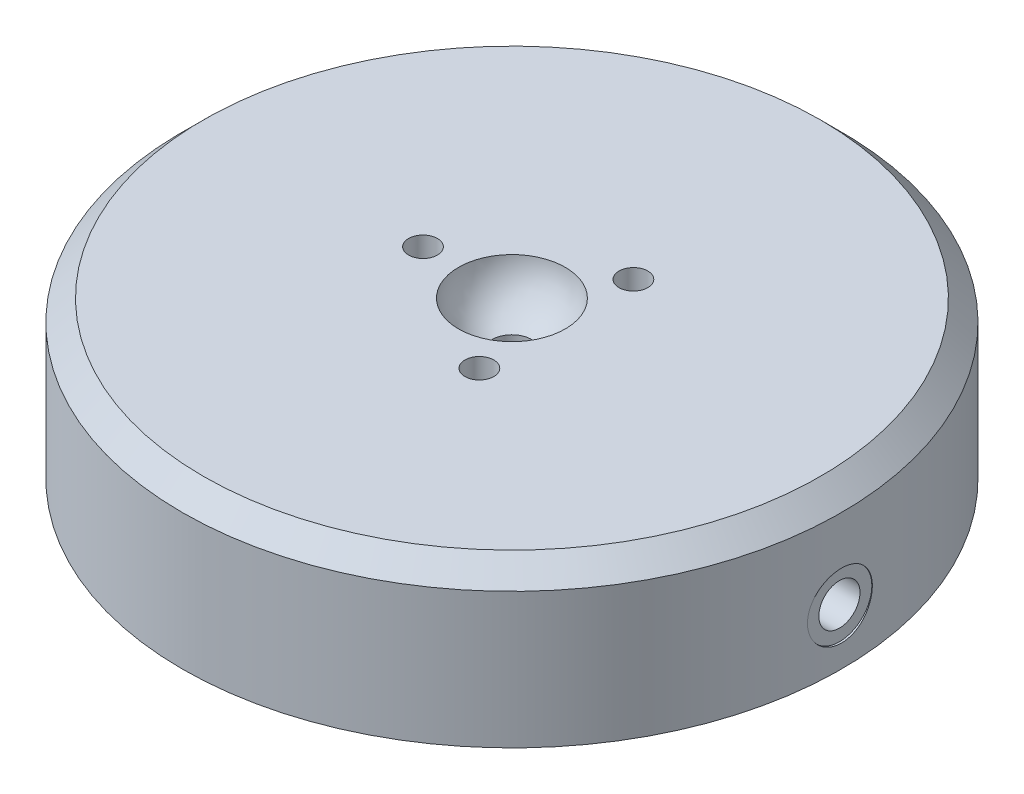
SolidWorks part; units mm, degrees
material "6061 Alloy"
ref_plane "Front Plane" through (0, 0, 0) normal (0, 0, 1) x (1, 0, 0)
ref_plane "Top Plane" through (0, 0, 0) normal (0, 1, 0) x (1, 0, 0)
ref_plane "Right Plane" through (0, 0, 0) normal (1, 0, 0) x (0, 0, -1)
sketch "Sketch1" plane through (0, 0, 0) normal (0, 1, 0) x (1, 0, 0)
  circle A0 centre (0, 0) radius 40.005
  dimension "D1" = 80.01
extrude "Extrude1" add sketch "Sketch1" along normal blind 18.9992
sketch "Sketch2" plane through (0, 0, 0) normal (0, -1, 0) x (1, 0, 0)
  circle A0 centre (0, 0) radius 38.1
  dimension "D1" = 76.2
hole_wizard "M5x0.8 Tapped Hole1" positions "3DSketch1" profile "Sketch4" tap size "M5x0.8" standard "Ansi Metric"
sketch3d "3DSketch1"
  point P0 (40.005, 6.6802, 0)
  dimension "D1" = 12.319
sketch "Sketch4" plane through (40.005, 6.6802, 0) normal (0, 1, 0) x (0, 0, -1)
  line L0 (0, 0) -> (0, 36.8218)
  line L1 (0, 36.8218) -> (2.1, 35.56)
  line L2 (2.1, 35.56) -> (2.1, 7.62)
  line L3 (2.1, 7.62) -> (2.5, 7.62)
  line L4 (2.5, 7.62) -> (2.5, 0)
  line L5 (2.5, 0) -> (0, 0)
  line L10 (0, 36.8218) -> (-2.1, 35.56) construction
  line L11 (0, -6.35) -> (0, 107.95) construction
  dimension "Tap Drill Dia." = 4.2
  dimension "Tap Drill Depth" = 35.56
  dimension "Thread Major Dia." = 5
  dimension "Thread Depth" = 7.62
  dimension "Drill Angle" = 118
hole_wizard "Hole3" positions "3DSketch4" profile "Sketch8" legacy
sketch3d "3DSketch4"
  line L0 (32.385, 6.6802, 0) -> (39.9268, 6.6802, 0) construction
  point P0 (40.005, 6.6802, 0)
sketch "Sketch8" plane through (40.005, 6.6802, 0) normal (0, 1, 0) x (0, 0, -1)
  line L0 (0, 0) -> (0, 7.4946)
  line L1 (0, 7.4946) -> (1.905, 6.35)
  line L2 (1.905, 6.35) -> (1.905, 0.254)
  line L3 (1.905, 0.254) -> (3.937, 0.254)
  line L4 (3.937, 0) -> (0, 0)
  line L5 (0, -11.3109) -> (0, 121.1557) construction
  line L6 (0, 7.4946) -> (-1.905, 6.35) construction
  line L7 (3.937, 0.254) -> (3.937, 0)
  dimension "Depth" = 6.35
  dimension "Drill Angle" = 118
  dimension "Diameter" = 3.81
  dimension "C-Bore Diameter" = 7.874
  dimension "C-Bore Depth" = 0.254
chamfer "Chamfer1" distance 2.54 angle 45 1 edges at (0, 18.9992, 40.005)
hole_wizard "M3.5x0.6 Tapped Hole1" positions "Sketch10" profile "Sketch9" tap size "M3.5x0.6" standard "Ansi Metric"
sketch "Sketch10" plane through (0, 18.9992, 0) normal (0, 1, 0) x (-1, 0, 0)
  point P0 (10.795, 0)
sketch "Sketch9" plane through (-10.795, 18.9992, 0) normal (1, 0, 0) x (0, 0, 1)
  line L0 (0, 0) -> (0, 10.5232)
  line L1 (0, 10.5232) -> (1.45, 9.652)
  line L2 (1.45, 9.652) -> (1.45, 6.35)
  line L3 (1.45, 6.35) -> (1.75, 6.35)
  line L4 (1.75, 6.35) -> (1.75, 0)
  line L5 (1.75, 0) -> (0, 0)
  line L10 (0, 10.5232) -> (-1.45, 9.652) construction
  line L11 (0, -6.35) -> (0, 107.95) construction
  dimension "Tap Drill Dia." = 2.9
  dimension "Tap Drill Depth" = 9.652
  dimension "Thread Major Dia." = 3.5
  dimension "Thread Depth" = 6.35
  dimension "Drill Angle" = 118
pattern_circular "CirPattern1" count 3 every 120 about axis through (0, 0, 0) along (0, 1, 0) of "M3.5x0.6 Tapped Hole1"
extrude "Extrude2" add sketch "Sketch2" along normal blind 1.0008
sketch "Sketch11" plane through (0, 0, 0) normal (0, 0, 1) x (1, 0, 0)
  line L0 (37.465, 18.9992) -> (-37.465, 18.9992) construction
  line L1 (0, 20.5785) -> (0, 0) construction
  line L2 (0, 18.9992) -> (0, 12.7508)
  line L3 (0, 12.7508) -> (2.3876, 12.7508)
  line L4 (2.3876, 12.7508) -> (2.3876, 13.4616)
  line L5 (0, 18.9992) -> (6.4801, 18.9992)
  arc A0 (2.3876, 13.4616) -> (6.4801, 18.9992) centre (0, 19.5072) ccw
  dimension "D1" = 6.5
  dimension "D2" = 0.508
  dimension "D3" = 6.2484
  dimension "D4" = 2.3876
revolve "Cut-Revolve1" cut sketch "Sketch11" angle 360 about L1
